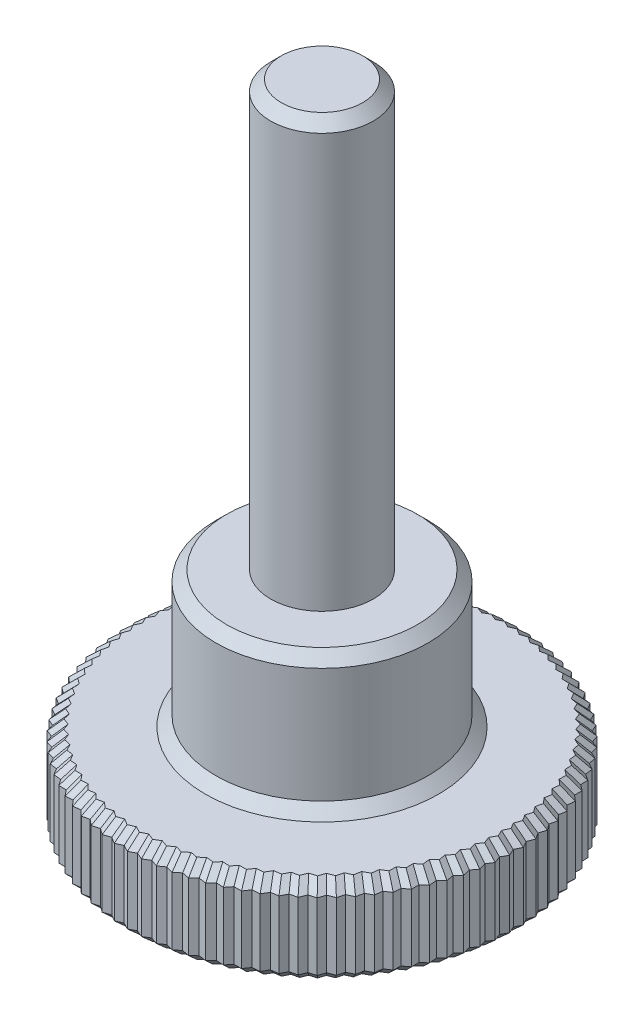
SolidWorks part; units mm, degrees
material "AISI 1020"
ref_plane "Front Plane" through (0, 0, 0) normal (0, 0, 1) x (1, 0, 0)
ref_plane "Top Plane" through (0, 0, 0) normal (0, 1, 0) x (1, 0, 0)
ref_plane "Right Plane" through (0, 0, 0) normal (1, 0, 0) x (0, 0, -1)
sketch "Sketch1" plane through (0, 0, 0) normal (0, 1, 0) x (1, 0, 0)
  line L0 (0, 0) -> (0, 5.5) construction
  line L1 (0, 5.5) -> (0.1887, 5.403)
  line L2 (0.3837, 5.4866) -> (0.1887, 5.403)
  line L3 (0.1919, 5.4966) -> (0, 0) construction
  line L4 (0.3837, 5.4866) -> (0.5651, 5.3767)
  line L5 (0.7655, 5.4465) -> (0.5651, 5.3767)
  line L6 (0.7655, 5.4465) -> (0.9388, 5.3241)
  line L7 (1.1435, 5.3798) -> (0.9388, 5.3241)
  line L8 (1.1435, 5.3798) -> (1.3079, 5.2457)
  line L9 (1.516, 5.2869) -> (1.3079, 5.2457)
  line L10 (1.516, 5.2869) -> (1.6706, 5.1417)
  line L11 (1.8811, 5.1683) -> (1.6706, 5.1417)
  line L12 (1.8811, 5.1683) -> (2.0252, 5.0126)
  line L13 (2.2371, 5.0245) -> (2.0252, 5.0126)
  line L14 (2.2371, 5.0245) -> (2.37, 4.8591)
  line L15 (2.5821, 4.8562) -> (2.37, 4.8591)
  line L16 (2.5821, 4.8562) -> (2.7031, 4.682)
  line L17 (2.9146, 4.6643) -> (2.7031, 4.682)
  line L18 (2.9146, 4.6643) -> (3.0232, 4.482)
  line L19 (3.2328, 4.4496) -> (3.0232, 4.482)
  line L20 (3.2328, 4.4496) -> (3.3284, 4.2602)
  line L21 (3.5353, 4.2132) -> (3.3284, 4.2602)
  line L22 (3.5353, 4.2132) -> (3.6175, 4.0176)
  line L23 (3.8206, 3.9564) -> (3.6175, 4.0176)
  line L24 (3.8206, 3.9564) -> (3.8889, 3.7555)
  line L25 (4.0873, 3.6802) -> (3.8889, 3.7555)
  line L26 (4.0873, 3.6802) -> (4.1414, 3.4751)
  line L27 (4.3341, 3.3861) -> (4.1414, 3.4751)
  line L28 (4.3341, 3.3861) -> (4.3738, 3.1777)
  line L29 (4.5597, 3.0756) -> (4.3738, 3.1777)
  line L30 (4.5597, 3.0756) -> (4.5848, 2.8649)
  line L31 (4.7631, 2.75) -> (4.5848, 2.8649)
  line L32 (4.7631, 2.75) -> (4.7735, 2.5381)
  line L33 (4.9434, 2.411) -> (4.7735, 2.5381)
  line L34 (4.9434, 2.411) -> (4.9389, 2.1989)
  line L35 (5.0995, 2.0603) -> (4.9389, 2.1989)
  line L36 (5.0995, 2.0603) -> (5.0802, 1.8491)
  line L37 (5.2308, 1.6996) -> (5.0802, 1.8491)
  line L38 (5.2308, 1.6996) -> (5.1968, 1.4902)
  line L39 (5.3366, 1.3306) -> (5.1968, 1.4902)
  line L40 (5.3366, 1.3306) -> (5.2881, 1.124)
  line L41 (5.4164, 0.9551) -> (5.2881, 1.124)
  line L42 (5.4164, 0.9551) -> (5.3537, 0.7524)
  line L43 (5.4699, 0.5749) -> (5.3537, 0.7524)
  line L44 (5.4699, 0.5749) -> (5.3931, 0.3771)
  line L45 (5.4966, 0.1919) -> (5.3931, 0.3771)
  line L46 (5.4966, 0.1919) -> (5.4063, 0)
  line L47 (5.4966, -0.1919) -> (5.4063, 0)
  line L48 (5.4966, -0.1919) -> (5.3931, -0.3771)
  line L49 (5.4699, -0.5749) -> (5.3931, -0.3771)
  line L50 (5.4699, -0.5749) -> (5.3537, -0.7524)
  line L51 (5.4164, -0.9551) -> (5.3537, -0.7524)
  line L52 (5.4164, -0.9551) -> (5.2881, -1.124)
  line L53 (5.3366, -1.3306) -> (5.2881, -1.124)
  line L54 (5.3366, -1.3306) -> (5.1968, -1.4902)
  line L55 (5.2308, -1.6996) -> (5.1968, -1.4902)
  line L56 (5.2308, -1.6996) -> (5.0802, -1.8491)
  line L57 (5.0995, -2.0603) -> (5.0802, -1.8491)
  line L58 (5.0995, -2.0603) -> (4.9389, -2.1989)
  line L59 (4.9434, -2.411) -> (4.9389, -2.1989)
  line L60 (4.9434, -2.411) -> (4.7735, -2.5381)
  line L61 (4.7631, -2.75) -> (4.7735, -2.5381)
  line L62 (4.7631, -2.75) -> (4.5848, -2.8649)
  line L63 (4.5597, -3.0756) -> (4.5848, -2.8649)
  line L64 (4.5597, -3.0756) -> (4.3738, -3.1777)
  line L65 (4.3341, -3.3861) -> (4.3738, -3.1777)
  line L66 (4.3341, -3.3861) -> (4.1414, -3.4751)
  line L67 (4.0873, -3.6802) -> (4.1414, -3.4751)
  line L68 (4.0873, -3.6802) -> (3.8889, -3.7555)
  line L69 (3.8206, -3.9564) -> (3.8889, -3.7555)
  line L70 (3.8206, -3.9564) -> (3.6175, -4.0176)
  line L71 (3.5353, -4.2132) -> (3.6175, -4.0176)
  line L72 (3.5353, -4.2132) -> (3.3284, -4.2602)
  line L73 (3.2328, -4.4496) -> (3.3284, -4.2602)
  line L74 (3.2328, -4.4496) -> (3.0232, -4.482)
  line L75 (2.9146, -4.6643) -> (3.0232, -4.482)
  line L76 (2.9146, -4.6643) -> (2.7031, -4.682)
  line L77 (2.5821, -4.8562) -> (2.7031, -4.682)
  line L78 (2.5821, -4.8562) -> (2.37, -4.8591)
  line L79 (2.2371, -5.0245) -> (2.37, -4.8591)
  line L80 (2.2371, -5.0245) -> (2.0252, -5.0126)
  line L81 (1.8811, -5.1683) -> (2.0252, -5.0126)
  line L82 (1.8811, -5.1683) -> (1.6706, -5.1417)
  line L83 (1.516, -5.2869) -> (1.6706, -5.1417)
  line L84 (1.516, -5.2869) -> (1.3079, -5.2457)
  line L85 (1.1435, -5.3798) -> (1.3079, -5.2457)
  line L86 (1.1435, -5.3798) -> (0.9388, -5.3241)
  line L87 (0.7655, -5.4465) -> (0.9388, -5.3241)
  line L88 (0.7655, -5.4465) -> (0.5651, -5.3767)
  line L89 (0.3837, -5.4866) -> (0.5651, -5.3767)
  line L90 (0.3837, -5.4866) -> (0.1887, -5.403)
  line L91 (0, -5.5) -> (0.1887, -5.403)
  line L92 (0, -5.5) -> (-0.1887, -5.403)
  line L93 (-0.3837, -5.4866) -> (-0.1887, -5.403)
  line L94 (-0.3837, -5.4866) -> (-0.5651, -5.3767)
  line L95 (-0.7655, -5.4465) -> (-0.5651, -5.3767)
  line L96 (-0.7655, -5.4465) -> (-0.9388, -5.3241)
  line L97 (-1.1435, -5.3798) -> (-0.9388, -5.3241)
  line L98 (-1.1435, -5.3798) -> (-1.3079, -5.2457)
  line L99 (-1.516, -5.2869) -> (-1.3079, -5.2457)
  line L100 (-1.516, -5.2869) -> (-1.6706, -5.1417)
  line L101 (-1.8811, -5.1683) -> (-1.6706, -5.1417)
  line L102 (-1.8811, -5.1683) -> (-2.0252, -5.0126)
  line L103 (-2.2371, -5.0245) -> (-2.0252, -5.0126)
  line L104 (-2.2371, -5.0245) -> (-2.37, -4.8591)
  line L105 (-2.5821, -4.8562) -> (-2.37, -4.8591)
  line L106 (-2.5821, -4.8562) -> (-2.7031, -4.682)
  line L107 (-2.9146, -4.6643) -> (-2.7031, -4.682)
  line L108 (-2.9146, -4.6643) -> (-3.0232, -4.482)
  line L109 (-3.2328, -4.4496) -> (-3.0232, -4.482)
  line L110 (-3.2328, -4.4496) -> (-3.3284, -4.2602)
  line L111 (-3.5353, -4.2132) -> (-3.3284, -4.2602)
  line L112 (-3.5353, -4.2132) -> (-3.6175, -4.0176)
  line L113 (-3.8206, -3.9564) -> (-3.6175, -4.0176)
  line L114 (-3.8206, -3.9564) -> (-3.8889, -3.7555)
  line L115 (-4.0873, -3.6802) -> (-3.8889, -3.7555)
  line L116 (-4.0873, -3.6802) -> (-4.1414, -3.4751)
  line L117 (-4.3341, -3.3861) -> (-4.1414, -3.4751)
  line L118 (-4.3341, -3.3861) -> (-4.3738, -3.1777)
  line L119 (-4.5597, -3.0756) -> (-4.3738, -3.1777)
  line L120 (-4.5597, -3.0756) -> (-4.5848, -2.8649)
  line L121 (-4.7631, -2.75) -> (-4.5848, -2.8649)
  line L122 (-4.7631, -2.75) -> (-4.7735, -2.5381)
  line L123 (-4.9434, -2.411) -> (-4.7735, -2.5381)
  line L124 (-4.9434, -2.411) -> (-4.9389, -2.1989)
  line L125 (-5.0995, -2.0603) -> (-4.9389, -2.1989)
  line L126 (-5.0995, -2.0603) -> (-5.0802, -1.8491)
  line L127 (-5.2308, -1.6996) -> (-5.0802, -1.8491)
  line L128 (-5.2308, -1.6996) -> (-5.1968, -1.4902)
  line L129 (-5.3366, -1.3306) -> (-5.1968, -1.4902)
  line L130 (-5.3366, -1.3306) -> (-5.2881, -1.124)
  line L131 (-5.4164, -0.9551) -> (-5.2881, -1.124)
  line L132 (-5.4164, -0.9551) -> (-5.3537, -0.7524)
  line L133 (-5.4699, -0.5749) -> (-5.3537, -0.7524)
  line L134 (-5.4699, -0.5749) -> (-5.3931, -0.3771)
  line L135 (-5.4966, -0.1919) -> (-5.3931, -0.3771)
  line L136 (-5.4966, -0.1919) -> (-5.4063, 0)
  line L137 (-5.4966, 0.1919) -> (-5.4063, 0)
  line L138 (-5.4966, 0.1919) -> (-5.3931, 0.3771)
  line L139 (-5.4699, 0.5749) -> (-5.3931, 0.3771)
  line L140 (-5.4699, 0.5749) -> (-5.3537, 0.7524)
  line L141 (-5.4164, 0.9551) -> (-5.3537, 0.7524)
  line L142 (-5.4164, 0.9551) -> (-5.2881, 1.124)
  line L143 (-5.3366, 1.3306) -> (-5.2881, 1.124)
  line L144 (-5.3366, 1.3306) -> (-5.1968, 1.4902)
  line L145 (-5.2308, 1.6996) -> (-5.1968, 1.4902)
  line L146 (-5.2308, 1.6996) -> (-5.0802, 1.8491)
  line L147 (-5.0995, 2.0603) -> (-5.0802, 1.8491)
  line L148 (-5.0995, 2.0603) -> (-4.9389, 2.1989)
  line L149 (-4.9434, 2.411) -> (-4.9389, 2.1989)
  line L150 (-4.9434, 2.411) -> (-4.7735, 2.5381)
  line L151 (-4.7631, 2.75) -> (-4.7735, 2.5381)
  line L152 (-4.7631, 2.75) -> (-4.5848, 2.8649)
  line L153 (-4.5597, 3.0756) -> (-4.5848, 2.8649)
  line L154 (-4.5597, 3.0756) -> (-4.3738, 3.1777)
  line L155 (-4.3341, 3.3861) -> (-4.3738, 3.1777)
  line L156 (-4.3341, 3.3861) -> (-4.1414, 3.4751)
  line L157 (-4.0873, 3.6802) -> (-4.1414, 3.4751)
  line L158 (-4.0873, 3.6802) -> (-3.8889, 3.7555)
  line L159 (-3.8206, 3.9564) -> (-3.8889, 3.7555)
  line L160 (-3.8206, 3.9564) -> (-3.6175, 4.0176)
  line L161 (-3.5353, 4.2132) -> (-3.6175, 4.0176)
  line L162 (-3.5353, 4.2132) -> (-3.3284, 4.2602)
  line L163 (-3.2328, 4.4496) -> (-3.3284, 4.2602)
  line L164 (-3.2328, 4.4496) -> (-3.0232, 4.482)
  line L165 (-2.9146, 4.6643) -> (-3.0232, 4.482)
  line L166 (-2.9146, 4.6643) -> (-2.7031, 4.682)
  line L167 (-2.5821, 4.8562) -> (-2.7031, 4.682)
  line L168 (-2.5821, 4.8562) -> (-2.37, 4.8591)
  line L169 (-2.2371, 5.0245) -> (-2.37, 4.8591)
  line L170 (-2.2371, 5.0245) -> (-2.0252, 5.0126)
  line L171 (-1.8811, 5.1683) -> (-2.0252, 5.0126)
  line L172 (-1.8811, 5.1683) -> (-1.6706, 5.1417)
  line L173 (-1.516, 5.2869) -> (-1.6706, 5.1417)
  line L174 (-1.516, 5.2869) -> (-1.3079, 5.2457)
  line L175 (-1.1435, 5.3798) -> (-1.3079, 5.2457)
  line L176 (-1.1435, 5.3798) -> (-0.9388, 5.3241)
  line L177 (-0.7655, 5.4465) -> (-0.9388, 5.3241)
  line L178 (-0.7655, 5.4465) -> (-0.5651, 5.3767)
  line L179 (-0.3837, 5.4866) -> (-0.5651, 5.3767)
  line L180 (-0.3837, 5.4866) -> (-0.1887, 5.403)
  line L181 (0, 5.5) -> (-0.1887, 5.403)
  circle A0 centre (0, 0) radius 5.5
  dimension "D1" = 11
  dimension "D2" = 2
  dimension "D3" = 90
extrude "Extrude1" add sketch "Sketch1" along normal blind 2.5 contours L1 L181 L180 L179 L178 L177 L176 L175 L174 L173 L172 L171 L170 L169 L168 L167 L166 L165 L164 L163 L162 L161 L160 L159 L158 L157 L156 L155 L154 L153 L152 L151 L150 L149 L148 L147 L146 L145 L144 L143 L142 L141 L140 L139 L138 L137 L136 L135 L134 L133 L132
sketch "Sketch2" plane through (0, 2.5, 0) normal (0, 1, 0) x (1, 0, 0)
  circle A0 centre (0, 0) radius 3
  dimension "D1" = 6
extrude "Extrude2" add sketch "Sketch2" along normal blind 3.85
sketch "Sketch3" plane through (0, 6.35, 0) normal (0, 1, 0) x (1, 0, 0)
  circle A0 centre (0, 0) radius 1.45
  dimension "D1" = 2.9
extrude "Extrude3" add sketch "Sketch3" along normal blind 12
cosmetic thread "Cosmetic Thread1" parameters "D2"=1.993
chamfer "Chamfer1" distance 0.3 angle 45 363 edges at (0.2862, 2.5, -5.4448) (0.4744, 2.5, -5.4316) (0.6653, 2.5, -5.4116) (0.8521, 2.5, -5.3853) (1.0412, 2.5, -5.352) (1.2257, 2.5, -5.3127) (1.412, 2.5, -5.2663) (1.5933, 2.5, -5.2143) (1.7759, 2.5, -5.155) (1.9532, 2.5, -5.0905) (2.1311, 2.5, -5.0186) (2.3035, 2.5, -4.9418) (2.476, 2.5, -4.8577) (2.6426, 2.5, -4.7691) (2.8088, 2.5, -4.6731) (2.9689, 2.5, -4.5731) (3.128, 2.5, -4.4658) (3.2806, 2.5, -4.3549) (3.4319, 2.5, -4.2367) (3.5764, 2.5, -4.1154) (3.7191, 2.5, -3.987) (3.8548, 2.5, -3.8559) (3.9881, 2.5, -3.7179) (4.1144, 2.5, -3.5777) (4.2378, 2.5, -3.4306) (4.3539, 2.5, -3.2819) (4.4667, 2.5, -3.1266) (4.5722, 2.5, -2.9702) (4.674, 2.5, -2.8074) (4.7683, 2.5, -2.644) (4.8584, 2.5, -2.4746) (4.9411, 2.5, -2.305) (5.0192, 2.5, -2.1296) (5.0899, 2.5, -1.9547) (5.1555, 2.5, -1.7743) (5.2138, 2.5, -1.5949) (5.2667, 2.5, -1.4104) (5.3124, 2.5, -1.2273) (5.3523, 2.5, -1.0395) (5.3851, 2.5, -0.8537) (5.4118, 2.5, -0.6637) (5.4315, 2.5, -0.476) (5.4449, 2.5, -0.2845) (5.4515, 2.5, -0.096) (5.4515, 2.5, 0.096) (5.4449, 2.5, 0.2845) (5.4315, 2.5, 0.476) (5.4118, 2.5, 0.6637) (5.3851, 2.5, 0.8537) (5.3523, 2.5, 1.0395) (5.3124, 2.5, 1.2273) (5.2667, 2.5, 1.4104) (5.2138, 2.5, 1.5949) (5.1555, 2.5, 1.7743) (5.0899, 2.5, 1.9547) (5.0192, 2.5, 2.1296) (4.9411, 2.5, 2.305) (4.8584, 2.5, 2.4746) (4.7683, 2.5, 2.644) (4.674, 2.5, 2.8074) (4.5722, 2.5, 2.9702) (4.4667, 2.5, 3.1266) (4.3539, 2.5, 3.2819) (4.2378, 2.5, 3.4306) (4.1144, 2.5, 3.5777) (3.9881, 2.5, 3.7179) (3.8548, 2.5, 3.8559) (3.7191, 2.5, 3.987) (3.5764, 2.5, 4.1154) (3.4319, 2.5, 4.2367) (3.2806, 2.5, 4.3549) (3.128, 2.5, 4.4658) (2.9689, 2.5, 4.5731) (2.8088, 2.5, 4.6731) (2.6426, 2.5, 4.7691) (2.476, 2.5, 4.8577) (2.3035, 2.5, 4.9418) (2.1311, 2.5, 5.0186) (1.9532, 2.5, 5.0905) (1.7759, 2.5, 5.155) (1.5933, 2.5, 5.2143) (1.412, 2.5, 5.2663) (1.2257, 2.5, 5.3127) (1.0412, 2.5, 5.352) (0.8521, 2.5, 5.3853) (0.6653, 2.5, 5.4116) (0.4744, 2.5, 5.4316) (0.2862, 2.5, 5.4448) (0.0943, 2.5, 5.4515) (-0.0943, 2.5, 5.4515) (-0.2862, 2.5, 5.4448) (-0.4744, 2.5, 5.4316) (-0.6653, 2.5, 5.4116) (-0.8521, 2.5, 5.3853) (-1.0412, 2.5, 5.352) (-1.2257, 2.5, 5.3127) (-1.412, 2.5, 5.2663) (-1.5933, 2.5, 5.2143) (-1.7759, 2.5, 5.155) (-1.9532, 2.5, 5.0905) (-2.1311, 2.5, 5.0186) (-2.3035, 2.5, 4.9418) (-2.476, 2.5, 4.8577) (-2.6426, 2.5, 4.7691) (-2.8088, 2.5, 4.6731) (-2.9689, 2.5, 4.5731) (-3.128, 2.5, 4.4658) (-3.2806, 2.5, 4.3549) (-3.4319, 2.5, 4.2367) (-3.5764, 2.5, 4.1154) (-3.7191, 2.5, 3.987) (-3.8548, 2.5, 3.8559) (-3.9881, 2.5, 3.7179) (-4.1144, 2.5, 3.5777) (-4.2378, 2.5, 3.4306) (-4.3539, 2.5, 3.2819) (-4.4667, 2.5, 3.1266) (-4.5722, 2.5, 2.9702) (-4.674, 2.5, 2.8074) (-4.7683, 2.5, 2.644) (-4.8584, 2.5, 2.4746) (-4.9411, 2.5, 2.305) (-5.0192, 2.5, 2.1296) (-5.0899, 2.5, 1.9547) (-5.1555, 2.5, 1.7743) (-5.2138, 2.5, 1.5949) (-5.2667, 2.5, 1.4104) (-5.3124, 2.5, 1.2273) (-5.3523, 2.5, 1.0395) (-5.3851, 2.5, 0.8537) (-5.4118, 2.5, 0.6637) (-5.4315, 2.5, 0.476) (-5.4449, 2.5, 0.2845) (-5.4515, 2.5, 0.096) (-5.4515, 2.5, -0.096) (-5.4449, 2.5, -0.2845) (-5.4315, 2.5, -0.476) (-5.4118, 2.5, -0.6637) (-5.3851, 2.5, -0.8537) (-5.3523, 2.5, -1.0395) (-5.3124, 2.5, -1.2273) (-5.2667, 2.5, -1.4104) (-5.2138, 2.5, -1.5949) (-5.1555, 2.5, -1.7743) (-5.0899, 2.5, -1.9547) (-5.0192, 2.5, -2.1296) (-4.9411, 2.5, -2.305) (-4.8584, 2.5, -2.4746) (-4.7683, 2.5, -2.644) (-4.674, 2.5, -2.8074) (-4.5722, 2.5, -2.9702) (-4.4667, 2.5, -3.1266) (-4.3539, 2.5, -3.2819) (-4.2378, 2.5, -3.4306) (-4.1144, 2.5, -3.5777) (-3.9881, 2.5, -3.7179) (-3.8548, 2.5, -3.8559) (-3.7191, 2.5, -3.987) (-3.5764, 2.5, -4.1154) (-3.4319, 2.5, -4.2367) (-3.2806, 2.5, -4.3549) (-3.128, 2.5, -4.4658) (-2.9689, 2.5, -4.5731) (-2.8088, 2.5, -4.6731) (-2.6426, 2.5, -4.7691) (-2.476, 2.5, -4.8577) (-2.3035, 2.5, -4.9418) (-2.1311, 2.5, -5.0186) (-1.9532, 2.5, -5.0905) (-1.7759, 2.5, -5.155) (-1.5933, 2.5, -5.2143) (-1.412, 2.5, -5.2663) (-1.2257, 2.5, -5.3127) (-1.0412, 2.5, -5.352) (-0.8521, 2.5, -5.3853) (-0.6653, 2.5, -5.4116) (-0.4744, 2.5, -5.4316) (-0.2862, 2.5, -5.4448) (-0.0943, 2.5, -5.4515) (0.0943, 2.5, -5.4515) (0, 2.5, 3) (-0.0943, 0, -5.4515) (-0.2862, 0, -5.4448) (-0.4744, 0, -5.4316) (-0.6653, 0, -5.4116) (-0.8521, 0, -5.3853) (-1.0412, 0, -5.352) (-1.2257, 0, -5.3127) (-1.412, 0, -5.2663) (-1.5933, 0, -5.2143) (-1.7759, 0, -5.155) (-1.9532, 0, -5.0905) (-2.1311, 0, -5.0186) (-2.3035, 0, -4.9418) (-2.476, 0, -4.8577) (-2.6426, 0, -4.7691) (-2.8088, 0, -4.6731) (-2.9689, 0, -4.5731) (-3.128, 0, -4.4658) (-3.2806, 0, -4.3549) (-3.4319, 0, -4.2367) (-3.5764, 0, -4.1154) (-3.7191, 0, -3.987) (-3.8548, 0, -3.8559) (-3.9881, 0, -3.7179) (-4.1144, 0, -3.5777) (-4.2378, 0, -3.4306) (-4.3539, 0, -3.2819) (-4.4667, 0, -3.1266) (-4.5722, 0, -2.9702) (-4.674, 0, -2.8074) (-4.7683, 0, -2.644) (-4.8584, 0, -2.4746) (-4.9411, 0, -2.305) (-5.0192, 0, -2.1296) (-5.0899, 0, -1.9547) (-5.1555, 0, -1.7743) (-5.2138, 0, -1.5949) (-5.2667, 0, -1.4104) (-5.3124, 0, -1.2273) (-5.3523, 0, -1.0395) (-5.3851, 0, -0.8537) (-5.4118, 0, -0.6637) (-5.4315, 0, -0.476) (-5.4449, 0, -0.2845) (-5.4515, 0, -0.096) (-5.4515, 0, 0.096) (-5.4449, 0, 0.2845) (-5.4315, 0, 0.476) (-5.4118, 0, 0.6637) (-5.3851, 0, 0.8537) (-5.3523, 0, 1.0395) (-5.3124, 0, 1.2273) (-5.2667, 0, 1.4104) (-5.2138, 0, 1.5949) (-5.1555, 0, 1.7743) (-5.0899, 0, 1.9547) (-5.0192, 0, 2.1296) (-4.9411, 0, 2.305) (-4.8584, 0, 2.4746) (-4.7683, 0, 2.644) (-4.674, 0, 2.8074) (-4.5722, 0, 2.9702) (-4.4667, 0, 3.1266) (-4.3539, 0, 3.2819) (-4.2378, 0, 3.4306) (-4.1144, 0, 3.5777) (-3.9881, 0, 3.7179) (-3.8548, 0, 3.8559) (-3.7191, 0, 3.987) (-3.5764, 0, 4.1154) (-3.4319, 0, 4.2367) (-3.2806, 0, 4.3549) (-3.128, 0, 4.4658) (-2.9689, 0, 4.5731) (-2.8088, 0, 4.6731) (-2.6426, 0, 4.7691) (-2.476, 0, 4.8577) (-2.3035, 0, 4.9418) (-2.1311, 0, 5.0186) (-1.9532, 0, 5.0905) (-1.7759, 0, 5.155) (-1.5933, 0, 5.2143) (-1.412, 0, 5.2663) (-1.2257, 0, 5.3127) (-1.0412, 0, 5.352) (-0.8521, 0, 5.3853) (-0.6653, 0, 5.4116) (-0.4744, 0, 5.4316) (-0.2862, 0, 5.4448) (-0.0943, 0, 5.4515) (0.0943, 0, 5.4515) (0.2862, 0, 5.4448) (0.4744, 0, 5.4316) (0.6653, 0, 5.4116) (0.8521, 0, 5.3853) (1.0412, 0, 5.352) (1.2257, 0, 5.3127) (1.412, 0, 5.2663) (1.5933, 0, 5.2143) (1.7759, 0, 5.155) (1.9532, 0, 5.0905) (2.1311, 0, 5.0186) (2.3035, 0, 4.9418) (2.476, 0, 4.8577) (2.6426, 0, 4.7691) (2.8088, 0, 4.6731) (2.9689, 0, 4.5731) (3.128, 0, 4.4658) (3.2806, 0, 4.3549) (3.4319, 0, 4.2367) (3.5764, 0, 4.1154) (3.7191, 0, 3.987) (3.8548, 0, 3.8559) (3.9881, 0, 3.7179) (4.1144, 0, 3.5777) (4.2378, 0, 3.4306) (4.3539, 0, 3.2819) (4.4667, 0, 3.1266) (4.5722, 0, 2.9702) (4.674, 0, 2.8074) (4.7683, 0, 2.644) (4.8584, 0, 2.4746) (4.9411, 0, 2.305) (5.0192, 0, 2.1296) (5.0899, 0, 1.9547) (5.1555, 0, 1.7743) (5.2138, 0, 1.5949) (5.2667, 0, 1.4104) (5.3124, 0, 1.2273) (5.3523, 0, 1.0395) (5.3851, 0, 0.8537) (5.4118, 0, 0.6637) (5.4315, 0, 0.476) (5.4449, 0, 0.2845) (5.4515, 0, 0.096) (5.4515, 0, -0.096) (5.4449, 0, -0.2845) (5.4315, 0, -0.476) (5.4118, 0, -0.6637) (5.3851, 0, -0.8537) (5.3523, 0, -1.0395) (5.3124, 0, -1.2273) (5.2667, 0, -1.4104) (5.2138, 0, -1.5949) (5.1555, 0, -1.7743) (5.0899, 0, -1.9547) (5.0192, 0, -2.1296) (4.9411, 0, -2.305) (4.8584, 0, -2.4746) (4.7683, 0, -2.644) (4.674, 0, -2.8074) (4.5722, 0, -2.9702) (4.4667, 0, -3.1266) (4.3539, 0, -3.2819) (4.2378, 0, -3.4306) (4.1144, 0, -3.5777) (3.9881, 0, -3.7179) (3.8548, 0, -3.8559) (3.7191, 0, -3.987) (3.5764, 0, -4.1154) (3.4319, 0, -4.2367) (3.2806, 0, -4.3549) (3.128, 0, -4.4658) (2.9689, 0, -4.5731) (2.8088, 0, -4.6731) (2.6426, 0, -4.7691) (2.476, 0, -4.8577) (2.3035, 0, -4.9418) (2.1311, 0, -5.0186) (1.9532, 0, -5.0905) (1.7759, 0, -5.155) (1.5933, 0, -5.2143) (1.412, 0, -5.2663) (1.2257, 0, -5.3127) (1.0412, 0, -5.352) (0.8521, 0, -5.3853) (0.6653, 0, -5.4116) (0.4744, 0, -5.4316) (0.2862, 0, -5.4448) (0.0943, 0, -5.4515) (0, 18.35, 1.45) (0, 6.35, 3)
